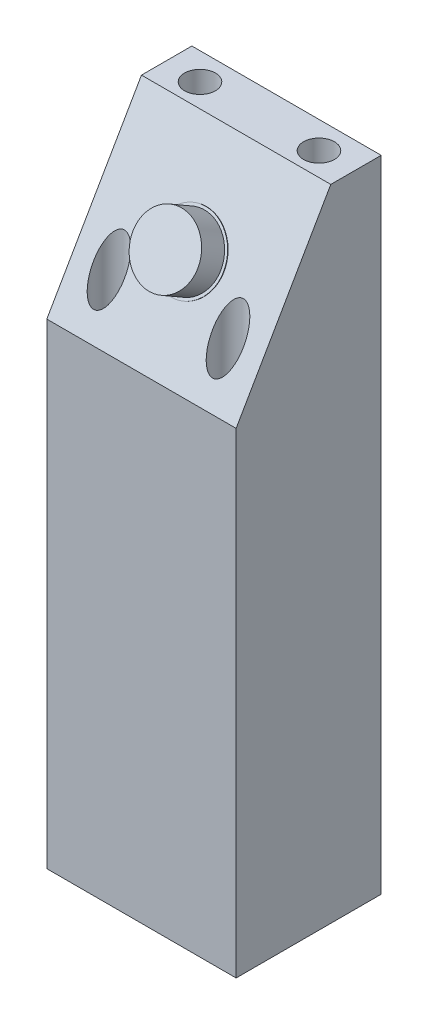
SolidWorks part; units mm, degrees
ref_plane "Ebene vorne" through (0, 0, 0) normal (0, 0, 1) x (1, 0, 0)
ref_plane "Ebene oben" through (0, 0, 0) normal (0, 1, 0) x (1, 0, 0)
ref_plane "Ebene rechts" through (0, 0, 0) normal (1, 0, 0) x (0, 0, -1)
sketch "Skizze1" plane through (0, 0, 0) normal (1, 0, 0) x (0, 0, -1)
  line L0 (0, 0) -> (17.5, 0)
  line L1 (0, 0) -> (0, 88)
  line L2 (0, 88) -> (17.5, 118.3109)
  line L3 (17.5, 118.3109) -> (17.5, 0) construction
  line L4 (17.5, 0) -> (26.82, 0)
  line L5 (26.82, 0) -> (26.82, 118.3109)
  line L6 (26.82, 118.3109) -> (17.5, 118.3109)
  dimension "D1" = 60
  dimension "D2" = 88
  dimension "D3" = 35
  dimension "D4" = 26.82
extrude "Aufsatz-Linear austragen1" add sketch "Skizze1" along normal blind 35
sketch "Skizze3" plane through (0, 22, 38.1051) normal (0, 0.5, 0.866) x (1, 0, 0)
  line L0 (0, 111.2102) -> (35, 76.2102) construction
  line L1 (17.5, 93.7102) -> (35, 111.2102) construction
  line L2 (35, 111.2102) -> (0, 111.2102) construction
  line L3 (35, 111.2102) -> (35, 76.2102) construction
  circle A0 centre (17.5, 93.7102) radius 6
  dimension "D1" = 12
extrude "Aufsatz-Linear austragen2" add sketch "Skizze3" along normal blind 5
sketch "Skizze4" plane through (0, 22, 38.1051) normal (0, 0.5, 0.866) x (1, 0, 0)
  circle A0 centre (17.5, 93.7102) radius 6.5
  dimension "D1" = 13
extrude "Aufsatz-Linear austragen3" add sketch "Skizze4" along normal blind 0.1
ref_plane "Ebene1" through (0, 88, 0) normal (0, -1, 0) x (-1, 0, 0)
ref_plane "Ebene2" through (0, 4.5, 0) normal (0, 1, 0) x (1, 0, 0)
sketch "Skizze7" plane through (0, 4.5, 0) normal (0, -1, 0) x (-1, 0, 0)
  line L0 (-35, 26.82) -> (0, 26.82) construction
  line L1 (-35, 0) -> (0, 26.82) construction
  line L2 (-17.5, 13.41) -> (-17.5, 26.82) construction
  line L4 (-17.5, 13.41) -> (-35, 13.41) construction
  line L5 (-35, 0) -> (-35, 26.82) construction
  circle A0 centre (-28.5, 5) radius 2.85
  circle A1 centre (-6.5, 5) radius 2.85
  circle A2 centre (-6.5, 21.82) radius 2.85
  circle A3 centre (-28.5, 21.82) radius 2.85
  dimension "D1" = 5.7
  dimension "D2" = 11
  dimension "D3" = 5
extrude "Schnitt-Linear austragen1" cut sketch "Skizze7" against normal through all
hole_wizard "Ø3.4 (3.4) Durchmesser Bohrung1" positions "3D-Skizze3" profile "Skizze8" hole size "Ø3.4" standard "DIN" end condition up to next
sketch3d "3D-Skizze3"
  line L0 (6.5, 101.5966, -5) -> (6.5, 4.5, -5) construction
  line L1 (6.5, 118.3109, -21.82) -> (6.5, 4.5, -21.82) construction
  line L2 (28.5, 118.3109, -21.82) -> (28.5, 4.5, -21.82) construction
  line L3 (28.5, 101.5966, -5) -> (28.5, 4.5, -5) construction
  point P0 (6.5, 4.5, -5)
  point P4 (6.5, 4.5, -21.82)
  point P8 (28.5, 4.5, -21.82)
  point P12 (28.5, 4.5, -5)
sketch "Skizze8" plane through (6.5, 4.5, -5) normal (1, 0, 0) x (0, 0, 1)
  line L0 (0, 0) -> (0, 4.5)
  line L1 (0, 4.5) -> (1.7, 4.5)
  line L2 (1.7, 4.5) -> (1.7, 0)
  line L5 (1.7, 0) -> (0, 0)
  line L11 (0, -6.35) -> (0, 107.95) construction
  dimension "Bohrerdurchmesser" = 3.4
  dimension "Bohrungstiefe" = 4.5
